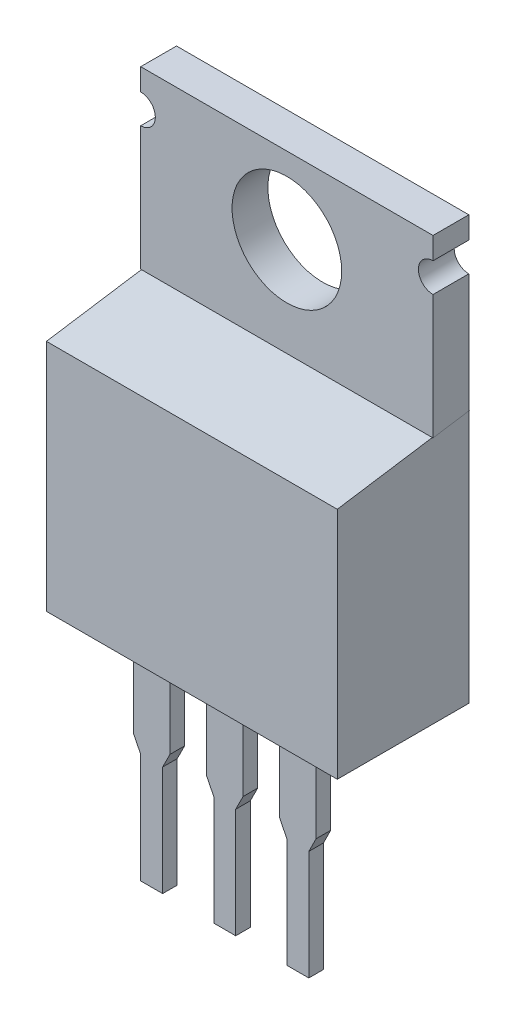
SolidWorks part; units mm, degrees
ref_plane "Front Plane" through (0, 0, 0) normal (0, 0, 1) x (1, 0, 0)
ref_plane "Top Plane" through (0, 0, 0) normal (0, 1, 0) x (1, 0, 0)
ref_plane "Right Plane" through (0, 0, 0) normal (1, 0, 0) x (0, 0, -1)
ref_plane "Plane2" through (0, 0, 1.397) normal (0, 0, 1) x (1, 0, 0)
ref_plane "Plane3" through (0, 3.81, 0) normal (0, 1, 0) x (-1, 0, 0)
ref_plane "Plane4" through (2.54, 0, 0) normal (1, 0, 0) x (0, 0, -1)
sketch "Sketch2" plane through (0, 3.81, 0) normal (0, 1, 0) x (-1, 0, 0)
  line L1 (2.54, -3.175) -> (-7.62, -3.175)
  line L2 (2.54, -3.175) -> (2.54, 1.397)
  line L3 (2.54, 1.397) -> (-7.62, 1.397)
  line L4 (-7.62, -3.175) -> (-7.62, 1.397)
  dimension "D1" = 10.16
  dimension "D2" = 4.572
  dimension "D3" = 7.62
  dimension "D4" = 3.175
extrude "Base-Extrude" add sketch "Sketch2" along normal blind 14.732
sketch "Sketch3" plane through (-2.54, 0, 0) normal (-1, 0, 0) x (0, 0, 1)
  line L0 (-1.905, 12.446) -> (-1.905, 18.542)
  line L1 (-1.905, 12.446) -> (1.397, 11.938)
  line L2 (-3.175, 18.542) -> (-3.175, 3.81) construction
  line L3 (-3.175, 18.542) -> (1.397, 18.542) construction
  line L5 (1.397, 18.542) -> (1.397, 3.81) construction
  dimension "D1" = 1.27
  dimension "D2" = 6.096
  dimension "D3" = 6.604
extrude "Cut-Extrude1" cut sketch "Sketch3" against normal through all and the other way through all
sketch "Sketch4" plane through (0, 0, -1.905) normal (0, 0, 1) x (1, 0, 0)
  line L0 (2.54, -50) -> (2.54, 50) construction
  line L1 (-2.54, 18.542) -> (7.62, 18.542) construction
  circle A0 centre (2.54, 15.875) radius 1.905
  dimension "D1" = 3.81
  dimension "D2" = 2.667
extrude "Cut-Extrude2" cut sketch "Sketch4" against normal blind 14.732
sketch "Sketch5" plane through (-2.54, 0, 0) normal (-1, 0, 0) x (0, 0, 1)
  line L0 (-1.905, 12.446) -> (1.397, 11.938) construction
  line L1 (-3.175, 18.542) -> (-3.175, 3.81) construction
  line L2 (-3.175, 3.81) -> (1.397, 3.81) construction
  line L3 (1.397, 11.938) -> (1.397, 3.81) construction
  line L4 (-3.175, 12.6414) -> (1.397, 11.938)
  line L5 (-3.175, 12.6414) -> (-3.175, 3.81)
  line L6 (-3.175, 3.81) -> (1.397, 3.81)
  line L7 (1.397, 11.938) -> (1.397, 3.81)
extrude "Cut-Extrude4" cut sketch "Sketch5" against normal blind 0.0254
sketch "Sketch6" plane through (7.62, 0, 0) normal (1, 0, 0) x (0, 0, -1)
  line L0 (-1.397, 11.938) -> (1.905, 12.446) construction
  line L1 (-1.397, 11.938) -> (-1.397, 3.81) construction
  line L2 (-1.397, 3.81) -> (3.175, 3.81) construction
  line L3 (3.175, 18.542) -> (3.175, 3.81) construction
  line L4 (-1.397, 11.938) -> (3.175, 12.6414)
  line L5 (-1.397, 11.938) -> (-1.397, 3.81)
  line L6 (-1.397, 3.81) -> (3.175, 3.81)
  line L7 (3.175, 12.6414) -> (3.175, 3.81)
extrude "Cut-Extrude5" cut sketch "Sketch6" against normal blind 0.0254
sketch "Sketch7" plane through (0, 0, -3.175) normal (0, 0, -1) x (-1, 0, 0)
  line L0 (-7.62, 18.542) -> (-7.62, 12.6414) construction
  line L1 (-7.62, 18.542) -> (2.54, 18.542) construction
  line L2 (2.54, 18.542) -> (2.54, 12.6414) construction
  line L3 (-7.62, 18.542) -> (-7.62, 12.6414)
  line L4 (-7.62, 18.542) -> (2.54, 18.542)
  line L5 (2.54, 18.542) -> (2.54, 12.6414)
  line L6 (-7.62, 12.6414) -> (-6.35, 12.6414)
  line L7 (-6.35, 12.6414) -> (-6.35, 7.112)
  line L8 (-6.35, 7.112) -> (1.27, 7.112)
  line L9 (1.27, 12.6414) -> (1.27, 7.112)
  line L10 (1.27, 12.6414) -> (2.54, 12.6414)
  line L11 (-7.5946, 3.81) -> (-7.5946, 12.6414) construction
  line L12 (-7.5946, 3.81) -> (2.5146, 3.81) construction
  line L13 (2.5146, 12.6414) -> (2.5146, 3.81) construction
  dimension "D1" = 1.2446
  dimension "D2" = 3.302
  dimension "D3" = 1.2446
extrude "Cut-Extrude6" cut sketch "Sketch7" against normal blind 0.0254
sketch "Sketch8" plane through (0, 0, -1.905) normal (0, 0, 1) x (1, 0, 0)
  line L0 (2.54, 15.8674) -> (2.54, 22.0486) construction
  line L1 (2.54, -50) -> (2.54, 50) construction
  line L2 (7.62, 12.446) -> (7.62, 18.542) construction
  line L3 (7.62, 16.764) -> (7.62, 17.78)
  line L4 (-2.54, 16.764) -> (-2.54, 17.78)
  line L5 (-2.54, 18.542) -> (-2.54, 12.446) construction
  line L6 (-2.54, 17.272) -> (9.7512, 17.272) construction
  line L7 (-2.54, 18.542) -> (7.62, 18.542) construction
  arc A0 (7.62, 17.78) -> (7.62, 16.764) centre (7.62, 17.272) ccw
  arc A1 (-2.54, 16.764) -> (-2.54, 17.78) centre (-2.54, 17.272) ccw
  dimension "D1" = 1.016
  dimension "D2" = 1.27
extrude "Cut-Extrude7" cut sketch "Sketch8" against normal blind 2.54
sketch "Sketch9" plane through (0, 0, 0) normal (0, 0, 1) x (1, 0, 0)
  line L0 (0, 3.81) -> (0, -3.81)
  line L1 (50, 3.81) -> (-50, 3.81) construction
  dimension "D1" = 7.62
extrude "Boss-Extrude-Thin1" add sketch "Sketch9" along normal mid plane 0.508 thin thin type mid plane wall 1.27
ref_plane "Board Plane" through (0.635, -3.81, 0.254) normal (0, -1, 0) x (1, 0, 0)
sketch "Sketch11" plane through (0, 0, 0.254) normal (0, 0, 1) x (1, 0, 0)
  line L0 (0.635, 0.508) -> (0.635, -3.81)
  line L1 (0.635, 3.81) -> (0.635, -3.81) construction
  line L2 (-0.635, 0.508) -> (-0.635, -3.81)
  line L3 (-0.635, 3.81) -> (-0.635, -3.81) construction
  line L4 (-0.381, 0) -> (-0.381, -3.81)
  line L5 (0.381, 0) -> (0.381, -3.81)
  line L6 (-49.365, -3.81) -> (50.635, -3.81) construction
  line L7 (-0.635, -3.81) -> (-0.381, -3.81)
  line L8 (0.381, -3.81) -> (0.635, -3.81)
  line L9 (0.381, 0) -> (0.635, 0.508)
  line L10 (-0.381, 0) -> (-0.635, 0.508)
  dimension "D1" = 0.762
  dimension "D2" = 0.254
  dimension "D3" = 4.318
extrude "Cut-Extrude8" cut sketch "Sketch11" against normal blind 1.27
pattern_linear "LPattern1" count 3 spacing 2.54 along (1, 0, 0) of "Boss-Extrude-Thin1", "Cut-Extrude8"
sketch "Component_Outline" plane through (0, 0, 0) normal (0, 1, 0) x (1, 0, 0)
  line L1 (-2.5146, -1.397) -> (7.5946, -1.397)
  line L2 (-2.5146, -1.397) -> (-2.5146, 3.175)
  line L3 (-2.5146, 3.175) -> (7.5946, 3.175)
  line L4 (7.5946, -1.397) -> (7.5946, 3.175)
